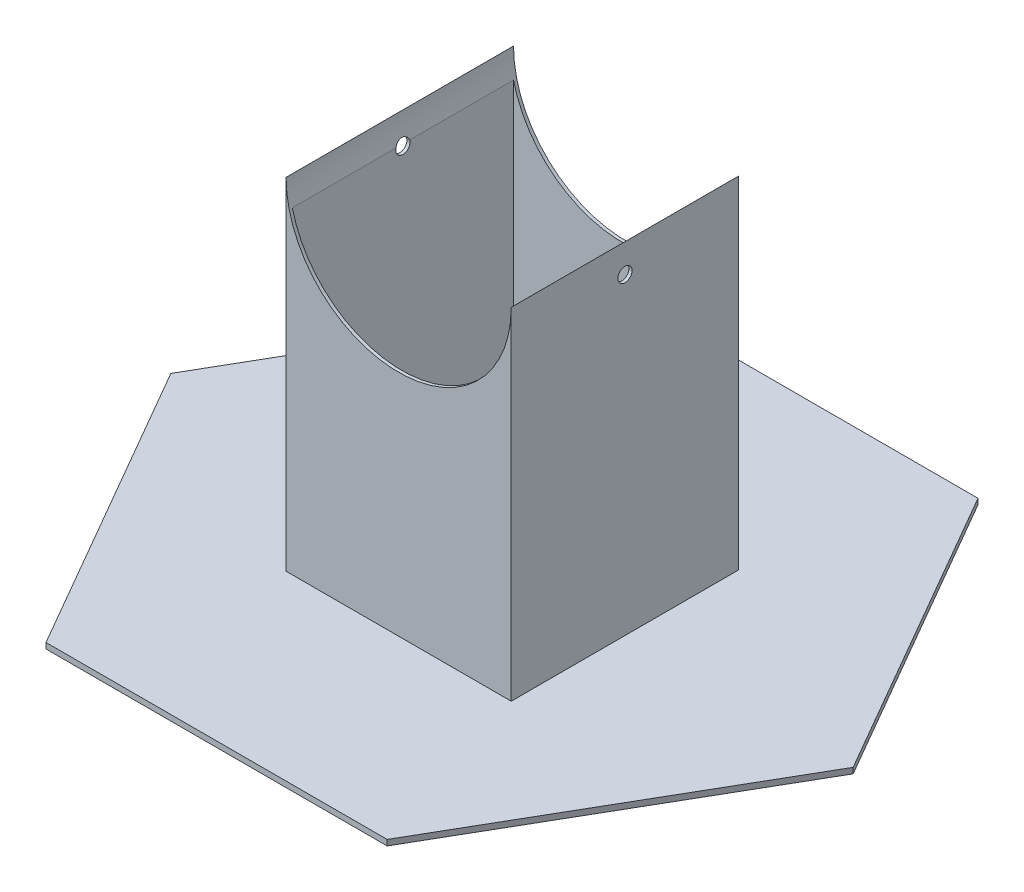
SolidWorks part; units mm, degrees
other "Weld Folder"
material "ASTM A36 Steel"
ref_plane "Front Plane" through (0, 0, 0) normal (0, 0, 1) x (1, 0, 0)
ref_plane "Top Plane" through (0, 0, 0) normal (0, 1, 0) x (1, 0, 0)
ref_plane "Right Plane" through (0, 0, 0) normal (1, 0, 0) x (0, 0, -1)
sketch "Sketch1" plane through (0, 0, 0) normal (0, 1, 0) x (1, 0, 0)
  line L21 (76.0355, -131.9823) -> (152.2355, 0)
  line L22 (152.2355, 0) -> (76.0355, 131.9823)
  line L23 (76.0355, 131.9823) -> (-76.3645, 131.9823)
  line L24 (-76.3645, 131.9823) -> (-152.5645, 0)
  line L25 (-152.5645, 0) -> (-76.3645, -131.9823)
  line L26 (-76.3645, -131.9823) -> (76.0355, -131.9823)
  dimension "D1" = 152.4
extrude "Boss-Extrude1" add sketch "Sketch1" along normal blind 2.54
sketch "Sketch2" plane through (0, 2.54, 0) normal (0, 1, 0) x (1, 0, 0)
  line L1 (-50.292, 50.8) -> (50.292, 50.8)
  line L2 (-50.292, 50.8) -> (-50.292, -50.8)
  line L3 (-50.292, -50.8) -> (50.292, -50.8)
  line L4 (50.292, 50.8) -> (50.292, -50.8)
  line L5 (-50.292, 50.8) -> (50.292, -50.8) construction
  line L6 (-50.292, -50.8) -> (50.292, 50.8) construction
  point P0 (0, 0)
  dimension "D1" = 100.584
  dimension "D2" = 101.6
extrude "Boss-Extrude2" add sketch "Sketch2" along normal blind 152.4
sketch "Sketch4" plane through (0, 154.94, 0) normal (0, 1, 0) x (1, 0, 0)
  line L1 (-48.8975, 49.4055) -> (48.8975, 49.4055)
  line L2 (-48.8975, 49.4055) -> (-48.8975, -49.4055)
  line L3 (-48.8975, -49.4055) -> (48.8975, -49.4055)
  line L4 (48.8975, 49.4055) -> (48.8975, -49.4055)
  line L5 (-48.8975, 49.4055) -> (48.8975, -49.4055) construction
  line L6 (-48.8975, -49.4055) -> (48.8975, 49.4055) construction
  point P0 (0, 0)
  dimension "D1" = 98.8111
  dimension "D2" = 97.7951
extrude "Cut-Extrude1" cut sketch "Sketch4" against normal blind 190.5
sketch "Sketch6" plane through (50.292, 0, 0) normal (1, 0, 0) x (0, 0, -1)
  line L1 (50.8, 154.94) -> (-50.8, 154.94) construction
  circle A0 centre (0, 142.24) radius 3.175
  point P2 (0, 0)
  dimension "D1" = 6.35
  dimension "D2" = 12.7
extrude "Cut-Extrude2" cut sketch "Sketch6" against normal through all
ref_plane "Actuated Plane" through (0, 205.74, 0) normal (0, 1, 0) x (1, 0, 0)
sketch "Sketch7" plane through (0, 0, -50.8) normal (0, 0, -1) x (-1, 0, 0)
  arc A0 (-50.292, 154.94) -> (50.292, 154.94) centre (0, 154.94) ccw
extrude "Cut-Extrude4" cut sketch "Sketch7" against normal through all and the other way through all
